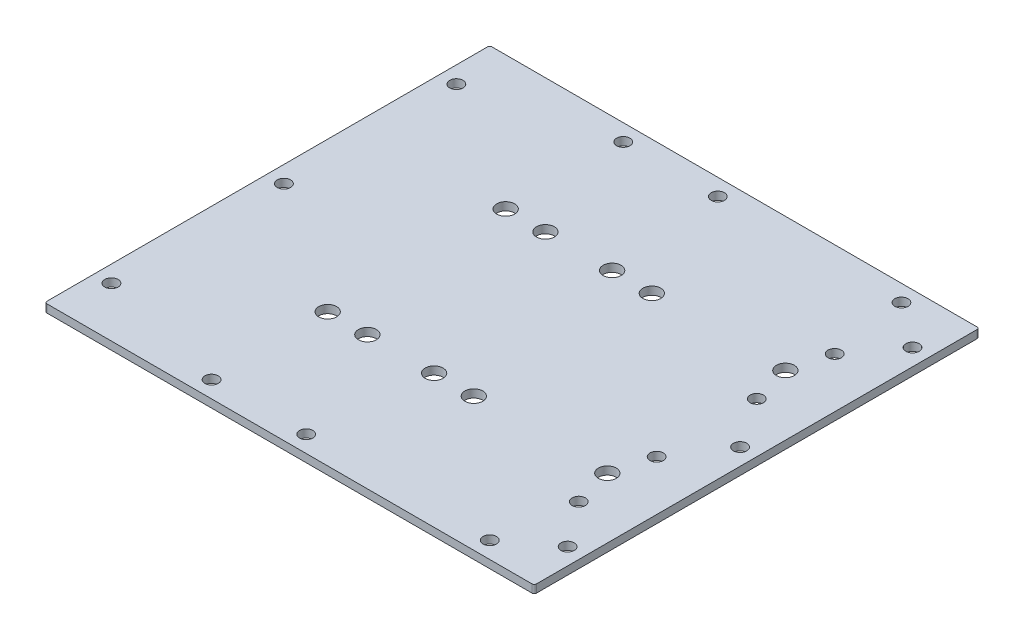
SolidWorks part; units mm, degrees
material "Alum Plate"
ref_plane "Front Plane" through (0, 0, 0) normal (0, 0, 1) x (1, 0, 0)
ref_plane "Top Plane" through (0, 0, 0) normal (0, 1, 0) x (1, 0, 0)
ref_plane "Right Plane" through (0, 0, 0) normal (1, 0, 0) x (0, 0, -1)
sketch "Sketch1" plane through (0, 0, 0) normal (0, 1, 0) x (1, 0, 0)
  line L0 (-15.875, -25.4) -> (-6.35, -25.4) construction
  line L1 (-69.85, -63.5) -> (69.85, -63.5)
  line L2 (-69.85, -63.5) -> (-69.85, 63.5)
  line L3 (-69.85, 63.5) -> (69.85, 63.5)
  line L4 (69.85, -63.5) -> (69.85, 63.5)
  line L5 (-69.85, -63.5) -> (69.85, 63.5) construction
  line L6 (-69.85, 63.5) -> (69.85, -63.5) construction
  line L11 (-6.35, -25.4) -> (3.175, -25.4) construction
  line L12 (-6.35, -25.4) -> (-6.35, 0) construction
  line L17 (-6.35, 0) -> (-6.35, 25.4) construction
  line L18 (-6.35, 25.4) -> (3.175, 25.4) construction
  line L23 (-6.35, 25.4) -> (-15.875, 25.4) construction
  line L24 (-15.875, -25.4) -> (-27.2034, -25.4) construction
  line L29 (3.175, -25.4) -> (14.5034, -25.4) construction
  line L30 (3.175, 25.4) -> (14.5034, 25.4) construction
  line L31 (-15.875, 25.4) -> (-27.2034, 25.4) construction
  line L32 (-46.2534, -63.5) -> (-46.2534, 63.5) construction
  line L33 (33.5534, -63.5) -> (33.5534, 63.5) construction
  line L34 (-46.2534, 0) -> (33.5534, 0) construction
  line L36 (14.5034, -25.4) -> (52.6034, -25.4) construction
  line L38 (14.5034, 25.4) -> (52.6034, 25.4) construction
  circle A9 centre (-15.875, 25.4) radius 2.5527
  circle A10 centre (3.175, 25.4) radius 2.5527
  circle A12 centre (-15.875, -25.4) radius 2.5527
  circle A13 centre (3.175, -25.4) radius 2.5527
  circle A14 centre (-27.2034, 25.4) radius 2.5527
  circle A15 centre (14.5034, 25.4) radius 2.5527
  circle A16 centre (14.5034, -25.4) radius 2.5527
  circle A17 centre (-27.2034, -25.4) radius 2.5527
  circle A18 centre (52.6034, 25.4) radius 2.5527
  circle A21 centre (52.6034, -25.4) radius 2.5527
  point P31 (33.5534, 25.4)
  dimension "D3" = 5.1054
  dimension "D1" = 127
  dimension "D2" = 139.7
  dimension "D4" = 50.8
  dimension "D6" = 9.525
  dimension "D7" = 23.5966
  dimension "D8" = 36.2966
  dimension "D9" = 38.1
extrude "Boss-Extrude1" add sketch "Sketch1" along normal blind 2.286
sketch "Sketch2" plane through (0, 0, 0) normal (0, -1, 0) x (1, 0, 0)
  line L0 (-65.0875, 49.2125) -> (-65.0875, 58.7375) construction
  line L1 (65.0875, 58.7375) -> (52.3875, 58.7375) construction
  line L2 (52.3875, 58.7375) -> (0, 58.7375) construction
  line L3 (65.0875, 58.7375) -> (65.0875, 49.2125) construction
  line L4 (65.0875, 49.2125) -> (69.85, 49.2125) construction
  line L5 (69.85, 63.5) -> (69.85, -63.5) construction
  line L6 (0, 58.7375) -> (0, 63.5) construction
  line L7 (-69.85, 63.5) -> (69.85, 63.5) construction
  line L8 (-65.0875, 49.2125) -> (-69.85, 49.2125) construction
  line L9 (-69.85, -63.5) -> (-69.85, 63.5) construction
  line L10 (-69.85, 0) -> (69.85, 0) construction
  line L11 (0, 58.7375) -> (-26.9875, 58.7375) construction
  line L12 (-26.9875, 58.7375) -> (-65.0875, 58.7375) construction
  line L13 (-26.9875, -58.7375) -> (-65.0875, -58.7375) construction
  line L14 (0, -58.7375) -> (-26.9875, -58.7375) construction
  line L15 (-65.0875, -49.2125) -> (-69.85, -49.2125) construction
  line L16 (0, -58.7375) -> (0, -63.5) construction
  line L17 (65.0875, -49.2125) -> (69.85, -49.2125) construction
  line L18 (65.0875, -58.7375) -> (65.0875, -49.2125) construction
  line L19 (52.3875, -58.7375) -> (0, -58.7375) construction
  line L20 (65.0875, -58.7375) -> (52.3875, -58.7375) construction
  line L21 (-65.0875, -49.2125) -> (-65.0875, -58.7375) construction
  line L26 (65.0875, 0) -> (69.85, 0) construction
  circle A1 centre (0, 58.7375) radius 1.8986
  circle A3 centre (-65.0875, 49.2125) radius 1.8987
  circle A9 centre (65.0875, 49.2125) radius 1.8987
  circle A15 centre (-65.0875, 0) radius 1.8987
  circle A16 centre (65.0875, 0) radius 1.8987
  circle A17 centre (52.3875, 58.7375) radius 1.8986
  circle A18 centre (-26.9875, 58.7375) radius 1.8986
  circle A19 centre (-26.9875, -58.7375) radius 1.8986
  circle A20 centre (52.3875, -58.7375) radius 1.8986
  circle A21 centre (65.0875, -49.2125) radius 1.8987
  circle A22 centre (-65.0875, -49.2125) radius 1.8987
  circle A23 centre (0, -58.7375) radius 1.8986
  dimension "D1" = 3.7973
  dimension "D2" = 4.7625
  dimension "D3" = 9.525
  dimension "D4" = 12.7
  dimension "D6" = 38.1
extrude "Cut-Extrude1" cut sketch "Sketch2" against normal through all
sketch "Sketch3" plane through (0, 2.286, 0) normal (0, 1, 0) x (1, 0, 0)
  line L0 (-69.85, 0) -> (-6.35, 0) construction
  line L1 (-21.59, -15.24) -> (8.89, -15.24) construction
  line L2 (-21.59, -15.24) -> (-21.59, 15.24) construction
  line L3 (-21.59, 15.24) -> (8.89, 15.24) construction
  line L4 (8.89, -15.24) -> (8.89, 15.24) construction
  line L5 (-21.59, -15.24) -> (8.89, 15.24) construction
  line L6 (-21.59, 15.24) -> (8.89, -15.24) construction
  line L7 (-69.85, 63.5) -> (-69.85, -63.5) construction
  circle A0 centre (-21.59, 15.24) radius 1.5875
  circle A1 centre (8.89, 15.24) radius 1.5875
  circle A2 centre (8.89, -15.24) radius 1.5875
  circle A3 centre (-21.59, -15.24) radius 1.5875
  point P0 (-6.35, 0)
  dimension "D2" = 3.175
  dimension "D1" = 30.48
  dimension "D3" = 63.5
extrude "Cut-Extrude2" [suppressed] cut sketch "Sketch3" against normal through all
fillet "Fillet1" radius 0.635 4 edges at (-69.85, 1.143, 63.5) (69.85, 1.143, 63.5) (-69.85, 1.143, -63.5) (69.85, 1.143, -63.5)
sketch "Sketch4" plane through (0, 0, 0) normal (0, -1, 0) x (1, 0, 0)
  line L0 (69.85, -36.5125) -> (55.5625, -36.5125) construction
  line L1 (69.85, 62.865) -> (69.85, -62.865) construction
  line L2 (55.5625, -36.5125) -> (55.5625, -14.2875) construction
  line L3 (55.5625, -14.2875) -> (55.5625, 14.2875) construction
  line L4 (55.5625, 14.2875) -> (55.5625, 36.5125) construction
  line L5 (55.5625, 36.5125) -> (69.85, 36.5125) construction
  line L6 (0, 0) -> (55.5625, 0) construction
  circle A0 centre (55.5625, 36.5125) radius 1.8987
  circle A1 centre (55.5625, 14.2875) radius 1.8987
  circle A2 centre (55.5625, -14.2875) radius 1.8987
  circle A3 centre (55.5625, -36.5125) radius 1.8987
  circle A4 centre (65.0875, 49.2125) radius 1.8987 construction
  dimension "D1" = 14.2875
  dimension "D2" = 22.225
  dimension "D3" = 28.575
extrude "Cut-Extrude3" cut sketch "Sketch4" against normal through all
